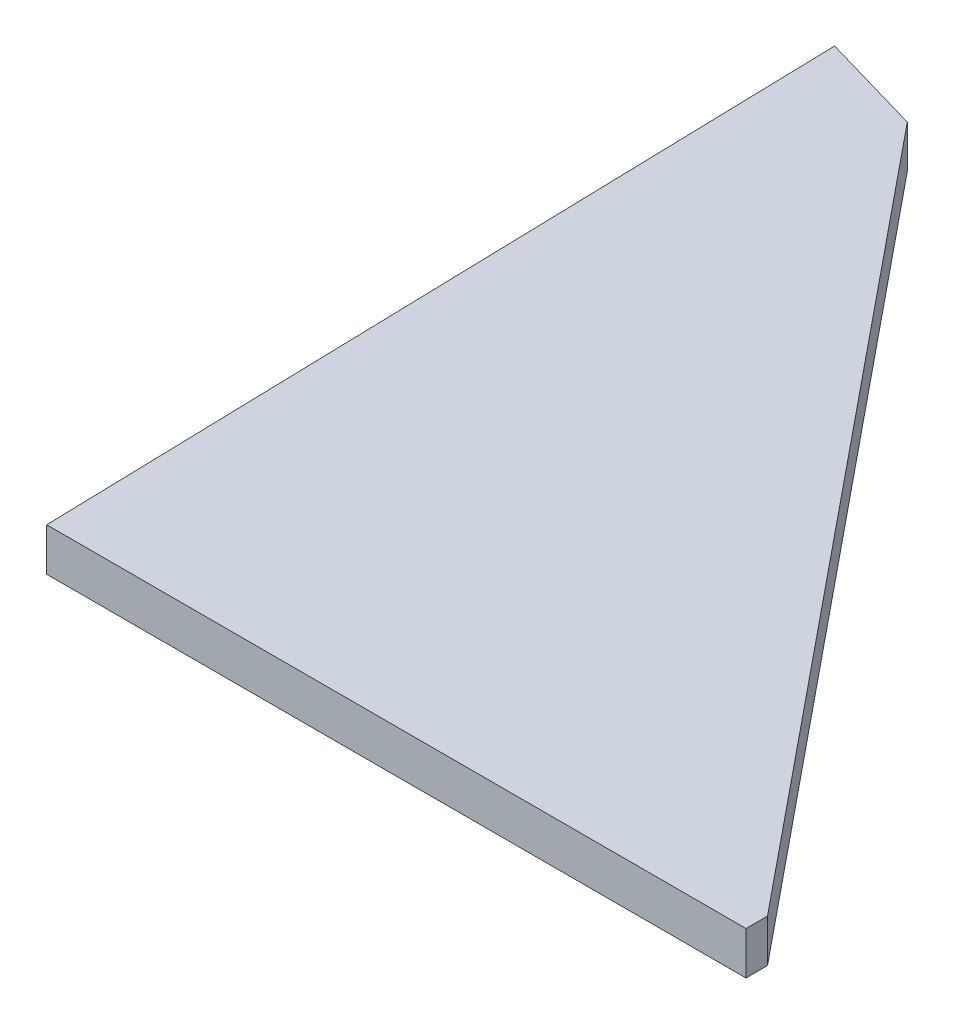
SolidWorks part; units mm, degrees
ref_plane "Plan de face" through (0, 0, 0) normal (0, 0, 1) x (1, 0, 0)
ref_plane "Plan de dessus" through (0, 0, 0) normal (0, 1, 0) x (1, 0, 0)
ref_plane "Plan de droite" through (0, 0, 0) normal (1, 0, 0) x (0, 0, -1)
sketch "Esquisse1" plane through (0, 0, 0) normal (0, 1, 0) x (1, 0, 0)
  line L0 (32.6229, 1.0044) -> (3.8053, 36.3438)
  line L1 (3.8053, 36.3438) -> (-0.9656, 37.7244)
  line L2 (-0.9656, 37.7244) -> (0, 0)
  line L3 (0, 0) -> (32.6229, 0)
  line L4 (32.6229, 0) -> (32.6229, 1.0044)
  point P5 (0, 0)
extrude "Boss.-Extru.1" add sketch "Esquisse1" along normal blind 2
